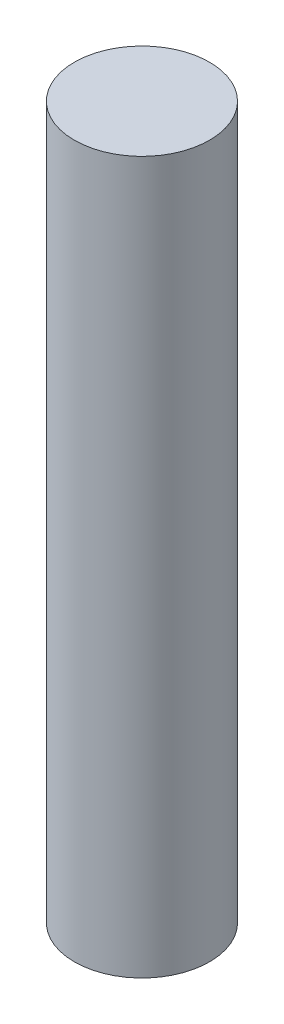
SolidWorks part; units mm, degrees
ref_plane "Front Plane" through (0, 0, 0) normal (0, 0, 1) x (1, 0, 0)
ref_plane "Top Plane" through (0, 0, 0) normal (0, 1, 0) x (1, 0, 0)
ref_plane "Right Plane" through (0, 0, 0) normal (1, 0, 0) x (0, 0, -1)
sketch "Sketch1" plane through (0, 0, 0) normal (0, 1, 0) x (1, 0, 0)
  circle A0 centre (1.9498, -0.2489) radius 4.826
  circle A1 centre (1.9498, -0.2489) radius 4.826 construction
extrude "Boss-Extrude1" add sketch "Sketch1" along normal blind 50.8
